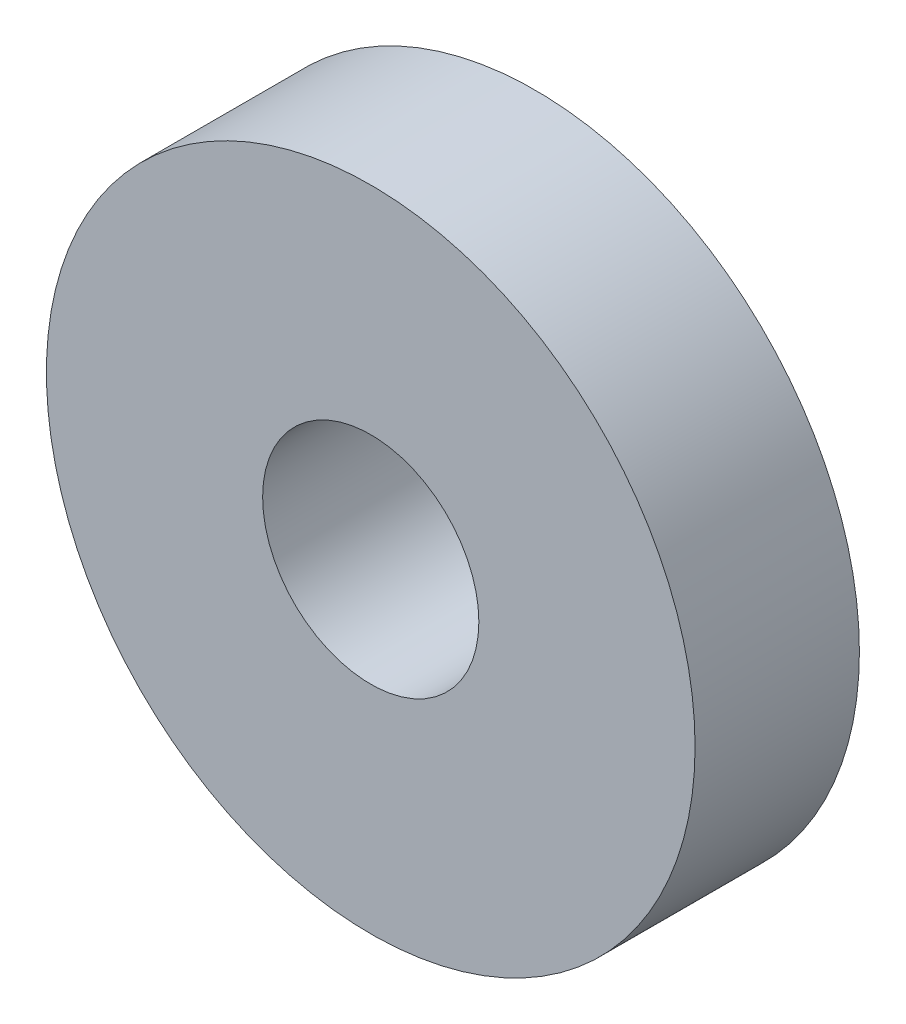
SolidWorks part; units mm, degrees
material "AISI 1020"
ref_plane "Спереди" through (0, 0, 0) normal (0, 0, 1) x (1, 0, 0)
ref_plane "Сверху" through (0, 0, 0) normal (0, 1, 0) x (1, 0, 0)
ref_plane "Справа" through (0, 0, 0) normal (1, 0, 0) x (0, 0, -1)
sketch "Эскиз1" plane through (0, 0, 0) normal (0, 0, 1) x (1, 0, 0)
  circle A0 centre (0, 0) radius 7.5
  circle A1 centre (0, 0) radius 2.5 construction
  circle A4 centre (0, 0) radius 2.5001
  circle A5 centre (0, 0) radius 2.5001
  dimension "D1" = 15
  dimension "D2" = 0.0001
extrude "Бобышка-Вытянуть1" add sketch "Эскиз1" against normal offset from surface (3.8 mm away) 0.1
